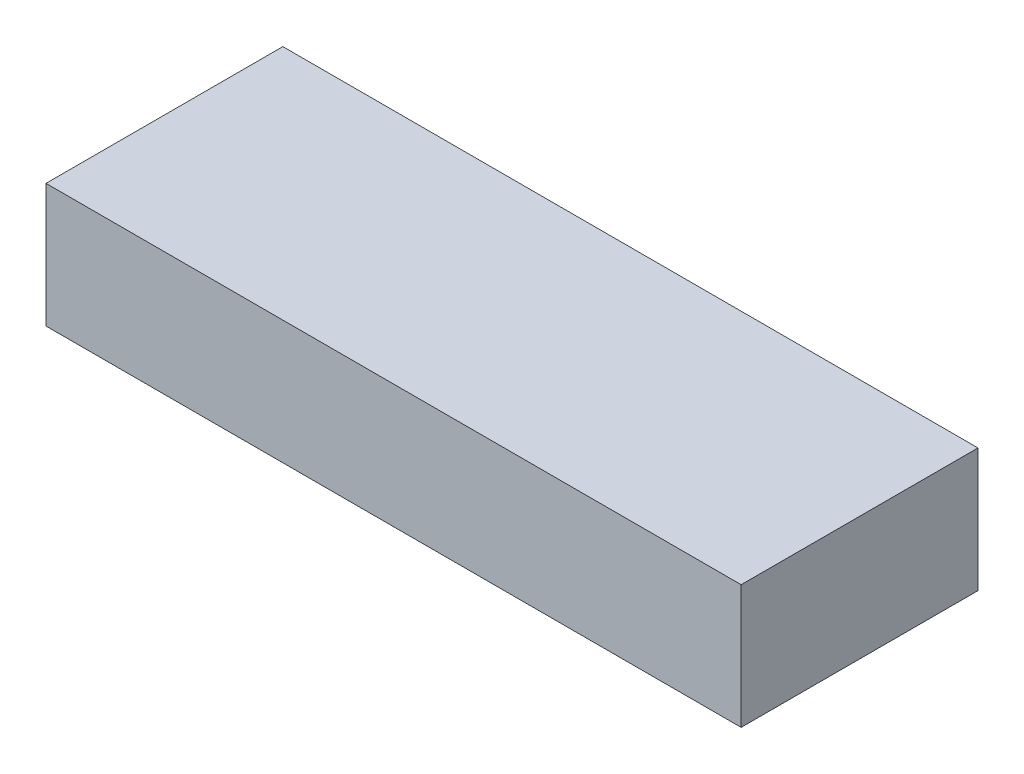
SolidWorks part; units mm, degrees
ref_plane "Front Plane" through (0, 0, 0) normal (0, 0, 1) x (1, 0, 0)
ref_plane "Top Plane" through (0, 0, 0) normal (0, 1, 0) x (1, 0, 0)
ref_plane "Right Plane" through (0, 0, 0) normal (1, 0, 0) x (0, 0, -1)
sketch "Sketch1" plane through (0, 0, 0) normal (0, 1, 0) x (1, 0, 0)
  line L1 (-67.5, -23) -> (67.5, -23)
  line L2 (-67.5, -23) -> (-67.5, 23)
  line L3 (-67.5, 23) -> (67.5, 23)
  line L4 (67.5, -23) -> (67.5, 23)
  line L5 (-67.5, -23) -> (67.5, 23) construction
  line L6 (-67.5, 23) -> (67.5, -23) construction
  point P0 (0, 0)
  dimension "D1" = 135
  dimension "D2" = 46
extrude "Boss-Extrude1" add sketch "Sketch1" along normal mid plane 24
